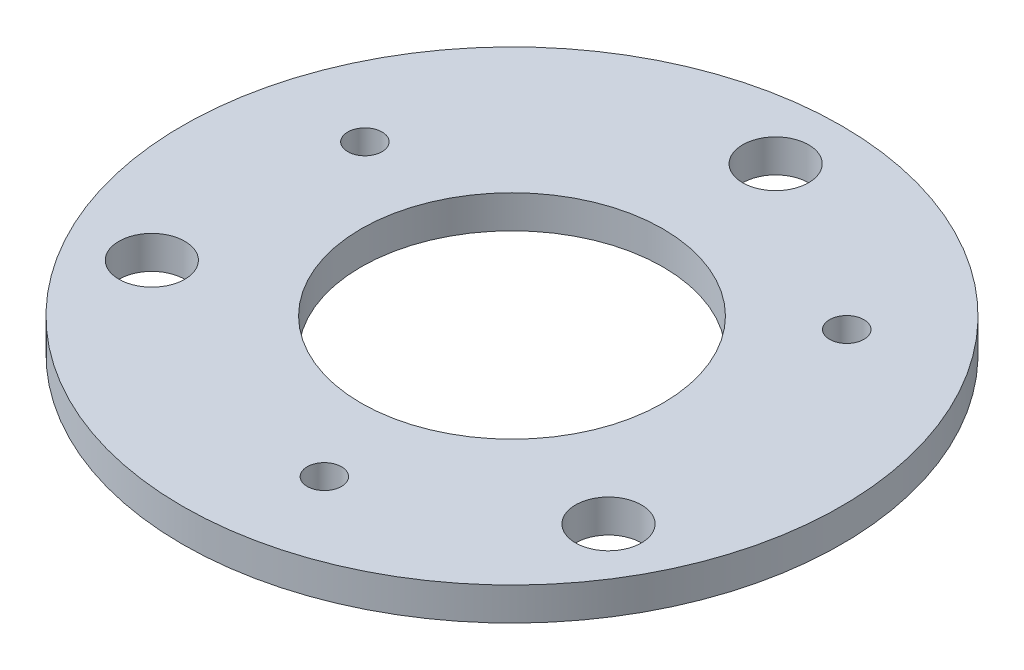
SolidWorks part; units mm, degrees
material "Maple"
ref_plane "Front Plane" through (0, 0, 0) normal (0, 0, 1) x (1, 0, 0)
ref_plane "Top Plane" through (0, 0, 0) normal (0, 1, 0) x (1, 0, 0)
ref_plane "Right Plane" through (0, 0, 0) normal (1, 0, 0) x (0, 0, -1)
sketch "Sketch1" plane through (0, 0, 0) normal (0, 1, 0) x (1, 0, 0)
  circle A0 centre (0, 0) radius 29.083
  circle A1 centre (0, 0) radius 63.5
  circle A2 centre (0, 50.8) radius 6.35
  circle A3 centre (43.9941, -25.4) radius 6.35
  circle A4 centre (-43.9941, -25.4) radius 6.35
  point P13 (0, 0)
  dimension "D1" = 58.166
  dimension "D2" = 127
  dimension "D3" = 12.7
  dimension "D4" = 50.8
  dimension "D5" = 3
extrude "Boss-Extrude1" add sketch "Sketch1" along normal blind 6.35
sketch "Sketch5" plane through (0, 6.35, 0) normal (0, 1, 0) x (1, 0, 0)
  line L0 (0, 0) -> (-43.2291, 14.885) construction
  line L1 (0, 0) -> (0, 57.15) construction
  circle A0 centre (-43.2291, 14.885) radius 3.302
  circle A1 centre (0, 50.8) radius 6.35 construction
  dimension "D1" = 6.604
  dimension "D2" = 71
  dimension "D3" = 45.72
extrude "Cut-Extrude4" cut sketch "Sketch5" against normal through all
pattern_circular "CirPattern2" count 3 over 360 about axis through (0, 0, 0) along (0, 1, 0) of "Cut-Extrude4"
